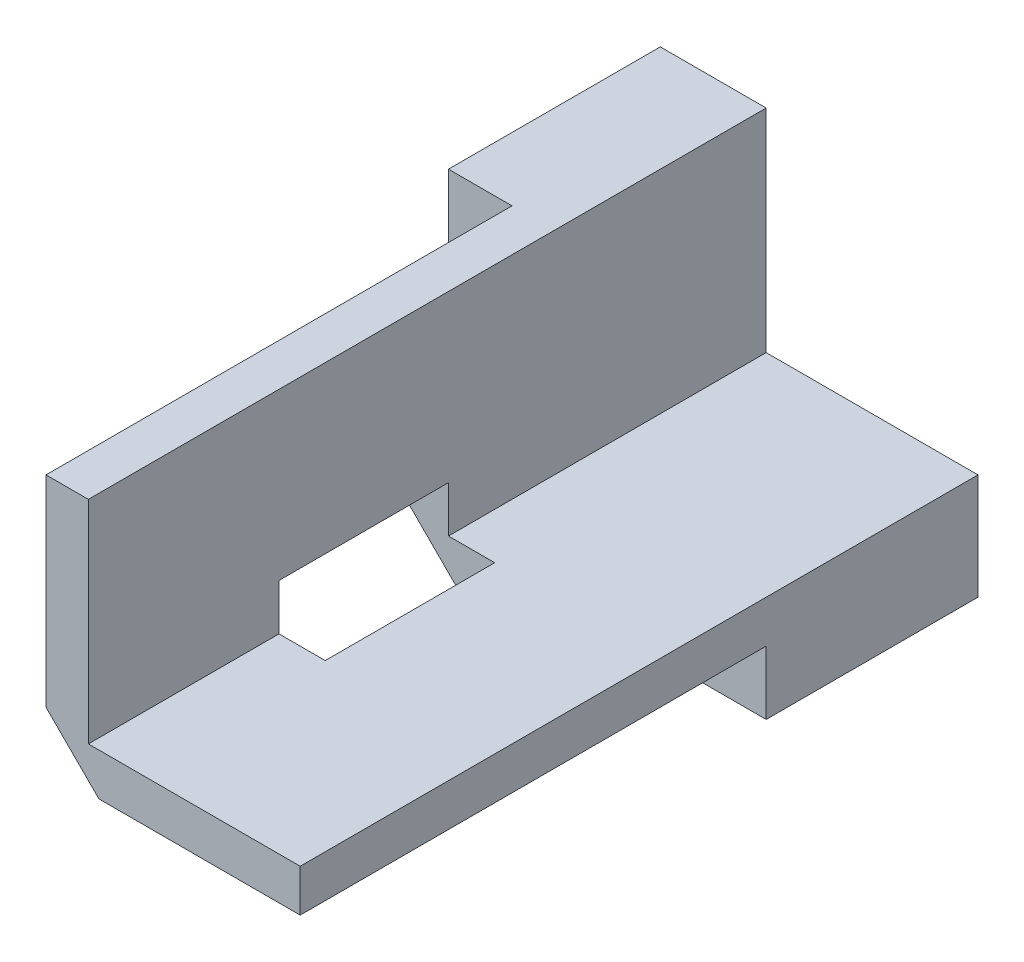
SolidWorks part; units mm, degrees
ref_plane "Спереди" through (0, 0, 0) normal (0, 0, 1) x (1, 0, 0)
ref_plane "Сверху" through (0, 0, 0) normal (0, 1, 0) x (1, 0, 0)
ref_plane "Справа" through (0, 0, 0) normal (1, 0, 0) x (0, 0, -1)
sketch "Эскиз1" plane through (0, 0, 0) normal (0, 0, 1) x (1, 0, 0)
  line L0 (0, 10) -> (0, 0)
  line L1 (0, 0) -> (10, 0)
  line L2 (-5, 10) -> (-5, -5)
  line L3 (-5, -5) -> (10, -5)
  line L4 (-5, 10) -> (0, 10)
  line L5 (10, 0) -> (10, -5)
  dimension "D2" = 15
  dimension "D1" = 5
extrude "Бобышка-Вытянуть1" add sketch "Эскиз1" along normal blind 32
chamfer "Фаска1" distance 2 angle 45 1 edges at (-5, -5, 16)
sketch "Эскиз2" plane through (0, 0, 32) normal (0, 0, 1) x (1, 0, 0)
  line L0 (-2, 10) -> (-2, -2)
  line L1 (0, 10) -> (-5, 10) construction
  line L2 (-2, -2) -> (10, -2)
  line L3 (10, -5) -> (10, 0) construction
  line L4 (0, 0) -> (0, 10) construction
  line L5 (10, 0) -> (0, 0) construction
  line M1 (-5, 10) -> (-5, -3)
  line M2 (-5, -3) -> (-3, -5)
  line M3 (-3, -5) -> (10, -5)
  line M4 (10, -5) -> (10, 0)
  line M7 (0, 10) -> (-5, 10)
  dimension "D1" = 2
  dimension "D2" = 2
extrude "Вырез-Вытянуть1" cut sketch "Эскиз2" against normal offset from surface (22 mm away) 10 contours L2 L0 M7 M1 M2 M3 M4 up to face at (1, 1, 0)
sketch "Эскиз3" plane through (-4, -4, 0) normal (-0.7071, -0.7071, 0) x (0, 0, 1)
  line L0 (10, 8.4853) -> (10, 0) construction
  line L1 (15, 14) -> (23, 14)
  line L2 (15, 14) -> (15, -14)
  line L3 (15, -14) -> (23, -14)
  line L4 (23, 14) -> (23, -14)
  line L5 (10, 0) -> (32, 0) construction
  dimension "D1" = 5
  dimension "D2" = 14
  dimension "D3" = 8
  dimension "D4" = 14
extrude "Вырез-Вытянуть2" cut sketch "Эскиз3" against normal blind 7.2
chamfer "Фаска2" distance 2.5 angle 45 2 edges at (-2, -2, 12.5) (-2, -2, 27.5)
hole_wizard "Отверстие обработанное метчиком #4-401" positions "Эскиз5" profile "Эскиз4" tap size "#4-40" standard "Ansi (в дюймах)" end condition up to next
sketch "Эскиз5" plane through (0, 0, 0) normal (0, 0, -1) x (-1, 0, 0)
  line L0 (0, 0) -> (0, 10) construction
  line L1 (-10, 0) -> (0, 0) construction
  point P0 (2, -2)
  dimension "D1" = 2
  dimension "D2" = 2
sketch "Эскиз4" plane through (-2, -2, 0) normal (1, 0, 0) x (0, 1, 0)
  line L0 (0, 0) -> (0, 10)
  line L1 (0, 10) -> (1.651, 10)
  line L2 (1.4224, 9.8399) -> (1.4224, 0.1601)
  line L3 (1.4224, 0.1601) -> (1.651, 0)
  line L5 (1.651, 0) -> (0, 0)
  line L6 (-1.4224, 0.1601) -> (-1.651, 0) construction
  line L7 (1.651, 10) -> (1.4224, 9.8399)
  line L8 (-1.651, 10) -> (-1.4224, 9.8399) construction
  line L11 (0, -6.35) -> (0, 107.95) construction
  dimension "Диаметр резьбы" = 2.8448
  dimension "Глубина проходного сверла" = 10
  dimension "Диаметр передней зенковки" = 3.302
  dimension "Угол передней зенковки" = 110
  dimension "Диаметр задней зенковки" = 3.302
  dimension "Угол задней зенковки" = 110
